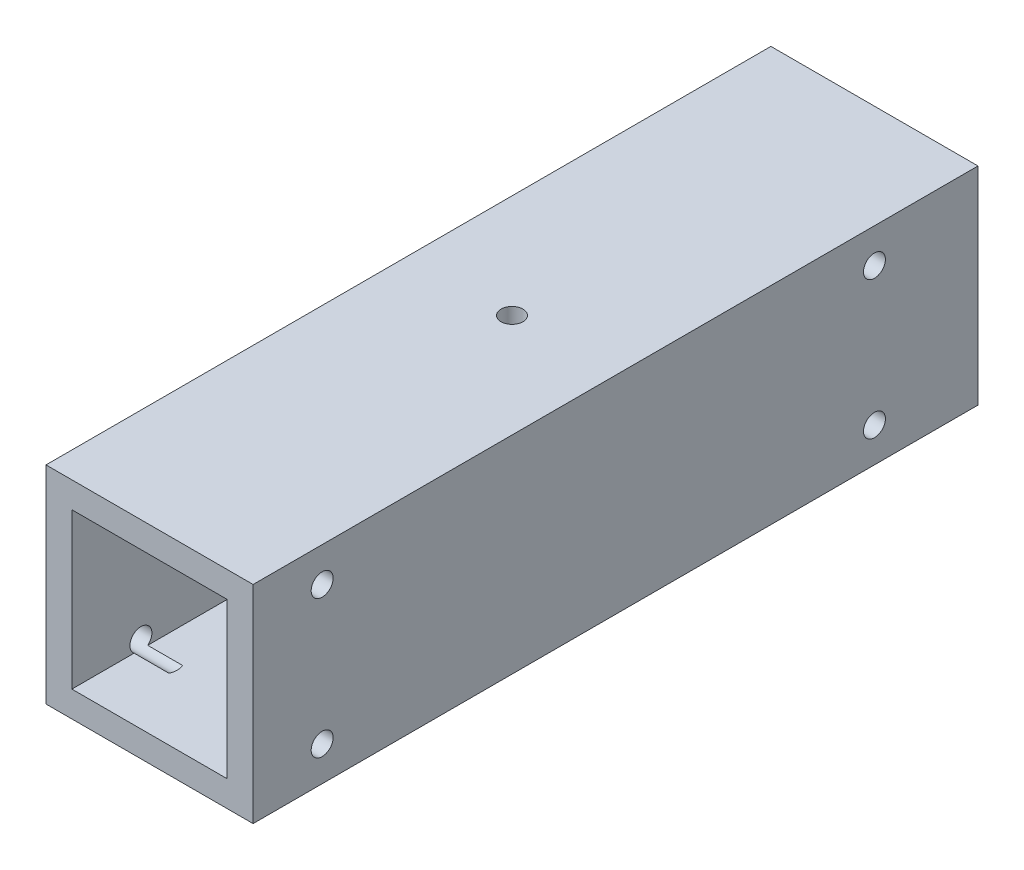
SolidWorks part; units mm, degrees
material "6061 Alloy"
ref_plane "Front Plane" through (0, 0, 0) normal (0, 0, 1) x (1, 0, 0)
ref_plane "Top Plane" through (0, 0, 0) normal (0, 1, 0) x (1, 0, 0)
ref_plane "Right Plane" through (0, 0, 0) normal (1, 0, 0) x (0, 0, -1)
sketch "Sketch1" plane through (0, 0, 0) normal (0, 1, 0) x (1, 0, 0)
  line L1 (-19.05, 66.675) -> (19.05, 66.675)
  line L2 (-19.05, 66.675) -> (-19.05, -66.675)
  line L3 (-19.05, -66.675) -> (19.05, -66.675)
  line L4 (19.05, 66.675) -> (19.05, -66.675)
  dimension "D1" = 19.05
  dimension "D2" = 19.05
  dimension "D3" = 66.675
  dimension "D4" = 66.675
extrude "Boss-Extrude1" add sketch "Sketch1" along normal mid plane 38.1
sketch "Sketch2" plane through (0, 0, 66.675) normal (0, 0, 1) x (1, 0, 0)
  line L0 (-19.05, 19.05) -> (-19.05, -19.05) construction
  line L1 (-14.2875, 14.2875) -> (14.2875, 14.2875)
  line L2 (-14.2875, 14.2875) -> (-14.2875, -14.2875)
  line L3 (-14.2875, -14.2875) -> (14.2875, -14.2875)
  line L4 (14.2875, 14.2875) -> (14.2875, -14.2875)
  line L5 (19.05, 19.05) -> (19.05, -19.05) construction
  line L6 (-19.05, -19.05) -> (19.05, -19.05) construction
  line L7 (-19.05, 19.05) -> (19.05, 19.05) construction
  dimension "D1" = 4.7625
  dimension "D2" = 4.7625
  dimension "D3" = 4.7625
  dimension "D4" = 4.7625
extrude "Cut-Extrude1" cut sketch "Sketch2" against normal through all
hole_wizard "#10-32 Tapped Hole1" positions "Sketch4" profile "Sketch3" tap size "#10-32" standard "ANSI Inch"
sketch "Sketch4" plane through (19.05, 0, 0) normal (1, 0, 0) x (0, 0, -1)
  line L0 (-66.675, 19.05) -> (-66.675, -19.05) construction
  line L1 (66.675, 19.05) -> (66.675, -19.05) construction
  point P0 (-53.975, -12.7)
  point P2 (-53.975, 12.7)
  point P4 (47.625, 12.7)
  point P6 (47.625, -12.7)
  dimension "D1" = 12.7
  dimension "D2" = 12.7
  dimension "D3" = 12.7
  dimension "D4" = 19.05
sketch "Sketch3" plane through (19.05, -12.7, 53.975) normal (0, 1, 0) x (0, 0, -1)
  line L0 (0, 0) -> (0, 12.3893)
  line L1 (0, 12.3893) -> (2.0193, 11.176)
  line L2 (2.0193, 11.176) -> (2.0193, 0)
  line L5 (2.0193, 0) -> (0, 0)
  line L10 (0, 12.3893) -> (-2.0193, 11.176) construction
  line L11 (0, -6.35) -> (0, 107.95) construction
  dimension "Tap Drill Dia." = 4.0386
  dimension "Tap Drill Depth" = 11.176
  dimension "Drill Angle" = 118
cosmetic thread "Hole Thread1" parameters "D1"=3.175, "D2"=4.826
cosmetic thread "Hole Thread2" parameters "D1"=3.175, "D2"=4.826
cosmetic thread "Hole Thread3" parameters "D1"=3.175, "D2"=4.826
cosmetic thread "Hole Thread4" parameters "D1"=3.175, "D2"=4.826
hole_wizard "#10-32 Tapped Hole2" positions "Sketch6" profile "Sketch7" tap size "#10-32" standard "ANSI Inch" end condition through all
sketch "Sketch6" plane through (0, 19.05, 0) normal (0, 1, 0) x (1, 0, 0)
  point P0 (0, 0)
sketch "Sketch7" plane through (0, 19.05, 0) normal (1, 0, 0) x (0, 0, 1)
  line L0 (0, 0) -> (0, 38.1)
  line L1 (0, 38.1) -> (2.0193, 38.1)
  line L2 (2.0193, 38.1) -> (2.0193, 0)
  line L5 (2.0193, 0) -> (0, 0)
  line L11 (0, -6.35) -> (0, 107.95) construction
  dimension "Thru Tap Drill Dia." = 4.0386
  dimension "Thru Tap Drill Depth" = 38.1
cosmetic thread "Hole Thread5" parameters "D2"=4.826
mirror "Mirror1" about plane through (0, 0, 0) normal (1, 0, 0) of "#10-32 Tapped Hole1"
